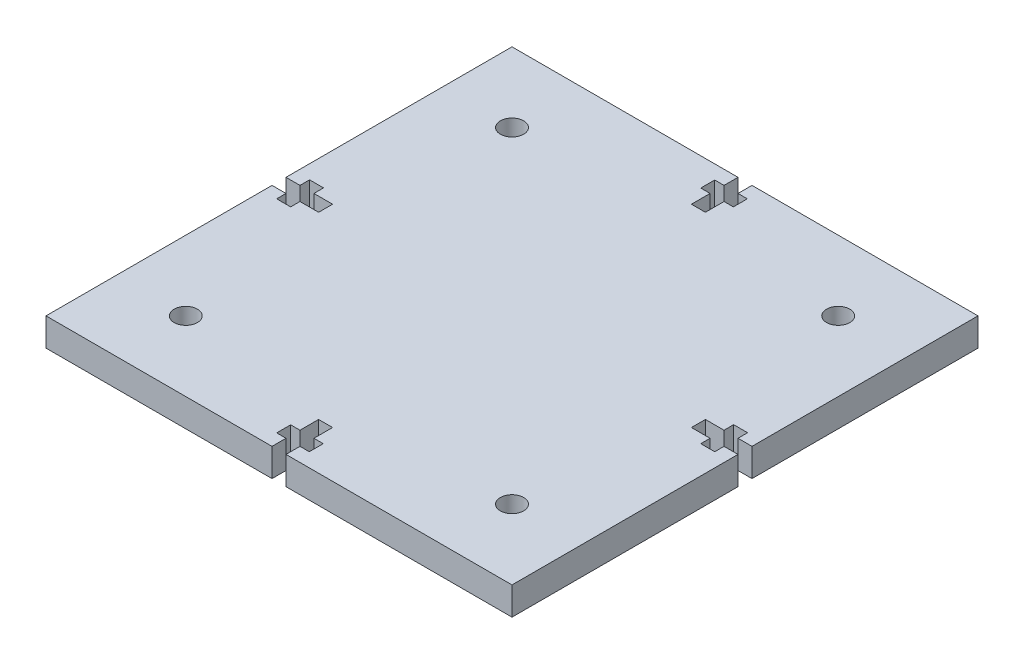
SolidWorks part; units mm, degrees
ref_plane "Front Plane" through (0, 0, 0) normal (0, 0, 1) x (1, 0, 0)
ref_plane "Top Plane" through (0, 0, 0) normal (0, 1, 0) x (1, 0, 0)
ref_plane "Right Plane" through (0, 0, 0) normal (1, 0, 0) x (0, 0, -1)
sketch "Sketch1" plane through (0, 0, 0) normal (0, 1, 0) x (1, 0, 0)
  line L0 (0, 0) -> (100, 0)
  line L1 (100, 0) -> (100, -100)
  line L2 (100, -100) -> (0, -100)
  line L3 (0, -100) -> (0, 0)
extrude "Boss-Extrude1" add sketch "Sketch1" along normal blind 6
sketch "Sketch2" plane through (0, 6, 0) normal (0, 1, 0) x (1, 0, 0)
  line L0 (50, 0) -> (50, -100) construction
  line L1 (100, 0) -> (0, 0) construction
  line L2 (0, -100) -> (100, -100) construction
  line L3 (0, -50) -> (100, -50) construction
  line L4 (0, 0) -> (0, -100) construction
  line L5 (100, -100) -> (100, 0) construction
  line L6 (48.5, 0) -> (51.5, 0)
  line L7 (51.5, 0) -> (51.5, -3)
  line L8 (51.5, -3) -> (53.5, -3)
  line L9 (53.5, -3) -> (53.5, -6)
  line L10 (53.5, -6) -> (51.5, -6)
  line L11 (51.5, -6) -> (51.5, -10)
  line L12 (51.5, -10) -> (48.5, -10)
  line L13 (48.5, -6) -> (48.5, -10)
  line L14 (46.5, -6) -> (48.5, -6)
  line L15 (46.5, -3) -> (46.5, -6)
  line L16 (48.5, -3) -> (46.5, -3)
  line L17 (48.5, 0) -> (48.5, -3)
  line L18 (48.5, -100) -> (48.5, -97)
  line L19 (48.5, -97) -> (46.5, -97)
  line L20 (46.5, -97) -> (46.5, -94)
  line L21 (46.5, -94) -> (48.5, -94)
  line L22 (48.5, -94) -> (48.5, -90)
  line L23 (51.5, -90) -> (48.5, -90)
  line L24 (51.5, -94) -> (51.5, -90)
  line L25 (53.5, -94) -> (51.5, -94)
  line L26 (53.5, -97) -> (53.5, -94)
  line L27 (51.5, -97) -> (53.5, -97)
  line L28 (51.5, -100) -> (51.5, -97)
  line L29 (48.5, -100) -> (51.5, -100)
  point P20 (50, -10)
  point P37 (50, -90)
extrude "Cut-Extrude1" cut sketch "Sketch2" against normal through all
sketch "Sketch3" plane through (0, 0, 0) normal (0, -1, 0) x (1, 0, 0)
  line L0 (50, 90) -> (50, 10) construction
  line L1 (51.5, 90) -> (48.5, 90) construction
  line L2 (48.5, 10) -> (51.5, 10) construction
  line L3 (0, 50) -> (100, 50) construction
  line L4 (0, 0) -> (0, 100) construction
  line L5 (100, 100) -> (100, 0) construction
  circle A0 centre (50, 50) radius 5
  circle A1 centre (85, 50) radius 2.5
  circle A2 centre (15, 50) radius 2.5
  circle A3 centre (50, 85) radius 2.5
  circle A4 centre (50, 16.6611) radius 2.7513
sketch "Sketch4" plane through (0, 0, 0) normal (0, -1, 0) x (-1, 0, 0)
  circle A1 centre (-15, -85) radius 2.5
  circle A2 centre (-85, -85) radius 2.5
  circle A3 centre (-85, -15) radius 2.5
  circle A4 centre (-15, -15) radius 2.5
extrude "Cut-Extrude3" cut sketch "Sketch4" against normal through all
sketch "Sketch5" plane through (0, 0, 0) normal (0, -1, 0) x (1, 0, 0)
  line L0 (0, 50) -> (0, 51.5)
  line L1 (0, 0) -> (0, 100) construction
  line L2 (0, 51.5) -> (3, 51.5)
  line L3 (3, 51.5) -> (3, 53.5)
  line L4 (3, 53.5) -> (6, 53.5)
  line L5 (6, 53.5) -> (6, 51.5)
  line L6 (6, 51.5) -> (10, 51.5)
  line L7 (10, 51.5) -> (10, 50)
  line L8 (0, 50) -> (100, 50) construction
  line L9 (10, 50) -> (10, 48.5)
  line L10 (10, 48.5) -> (6, 48.5)
  line L11 (6, 48.5) -> (6, 46.4394)
  line L12 (6, 46.4394) -> (3, 46.4394)
  line L13 (3, 46.4394) -> (3, 48.5)
  line L14 (3, 48.5) -> (0, 48.5)
  line L15 (0, 48.5) -> (0, 51.1936)
  line L16 (100, 50) -> (100, 51.5)
  line L17 (100, 100) -> (100, 0) construction
  line L18 (100, 51.5) -> (97, 51.5)
  line L19 (97, 51.5) -> (97, 53.5)
  line L20 (97, 53.5) -> (94, 53.5)
  line L21 (94, 53.5) -> (94, 51.5)
  line L22 (94, 51.5) -> (90, 51.5)
  line L23 (90, 51.5) -> (90, 50)
  line L24 (90, 50) -> (90, 48.5)
  line L25 (90, 48.5) -> (94, 48.5)
  line L26 (94, 48.5) -> (94, 46.4394)
  line L27 (94, 46.4394) -> (97, 46.4394)
  line L28 (97, 46.4394) -> (97, 48.5)
  line L29 (97, 48.5) -> (100, 48.5)
  line M17 (100, 0) -> (100, 100)
  line M31 (0, 100) -> (0, 0)
extrude "Cut-Extrude4" cut sketch "Sketch5" against normal blind 10 contours L14 L13 L12 L11 L10 L9 L7 L6 L5 L4 L3 L2 L0 M31 | L28 L29 L18 L19 L20 L21 L22 L23 L24 L25 L26 L27 M17
